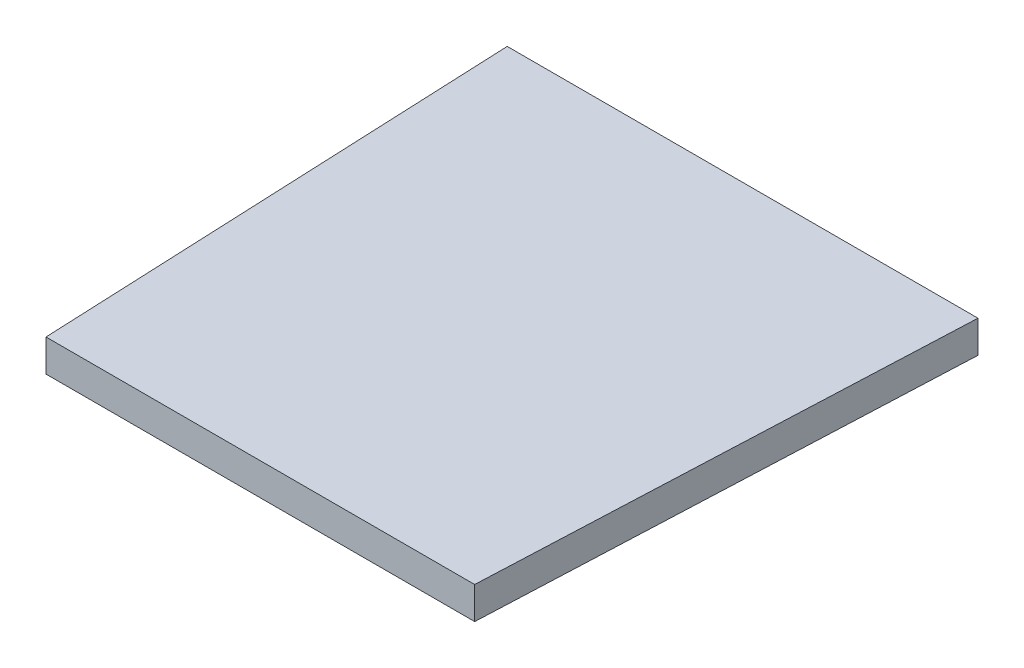
SolidWorks part; units mm, degrees
ref_plane "Front Plane" through (0, 0, 0) normal (0, 0, 1) x (1, 0, 0)
ref_plane "Top Plane" through (0, 0, 0) normal (0, 1, 0) x (1, 0, 0)
ref_plane "Right Plane" through (0, 0, 0) normal (1, 0, 0) x (0, 0, -1)
sketch "Sketch1" plane through (0, 0, 0) normal (0, 1, 0) x (1, 0, 0)
  line L0 (-21.9647, 100) -> (-20, 55)
  line L5 (-21.9647, 100) -> (0, 100)
  line L6 (0, 100) -> (0, 55)
  line L7 (0, 55) -> (-20, 55)
  point P4 (0, 77.5)
  dimension "D1" = 45
  dimension "D2" = 77.5
  dimension "D3" = 2.5
  dimension "D4" = 20
extrude "Boss-Extrude1" add sketch "Sketch1" along normal blind 3
mirror "Mirror2" about plane through (0, 0, 0) normal (1, 0, 0) of "Boss-Extrude1"
